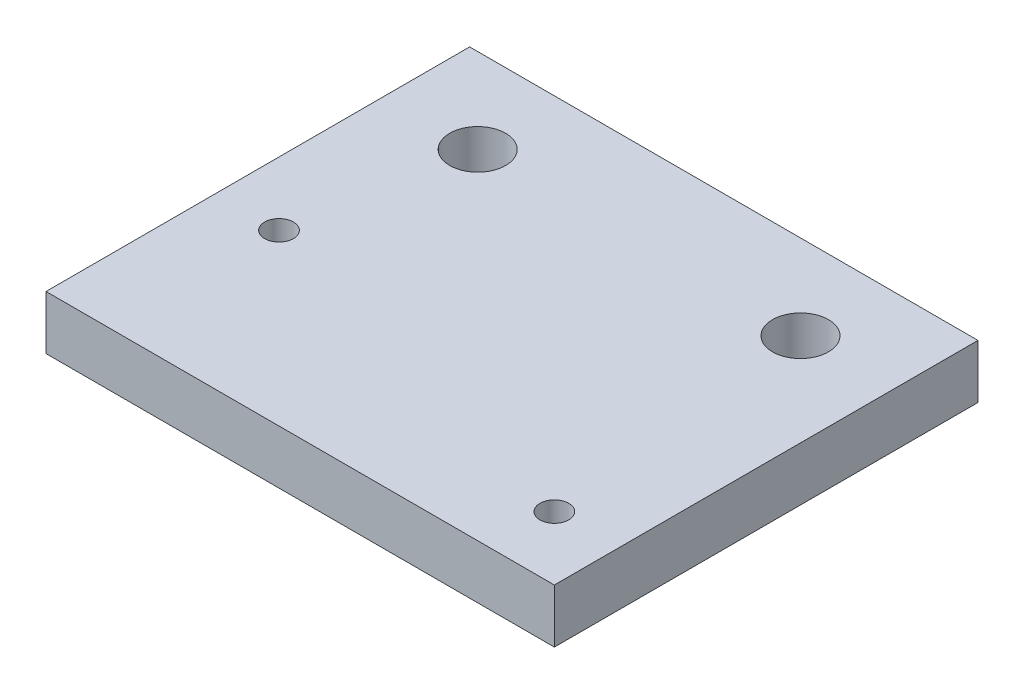
SolidWorks part; units mm, degrees
ref_plane "Front Plane" through (0, 0, 0) normal (0, 0, 1) x (1, 0, 0)
ref_plane "Top Plane" through (0, 0, 0) normal (0, 1, 0) x (1, 0, 0)
ref_plane "Right Plane" through (0, 0, 0) normal (1, 0, 0) x (0, 0, -1)
sketch "Sketch1" plane through (0, 0, 0) normal (0, 1, 0) x (1, 0, 0)
  line L0 (10.95, 40) -> (49.05, 40) construction
  line L1 (0, 50) -> (60, 50)
  line L2 (0, 50) -> (0, 0)
  line L3 (0, 0) -> (60, 0)
  line L4 (60, 50) -> (60, 0)
  line L5 (52.5, 20) -> (7.5, 20) construction
  circle A0 centre (10.95, 40) radius 3.3
  circle A1 centre (49.05, 40) radius 3.3
  circle A2 centre (7.5, 20) radius 1.7
  circle A3 centre (52.5, 7.5) radius 1.7
  point P9 (0, 0)
  point P15 (0, 0)
  point P16 (46.4465, 55)
  point P17 (30, 40)
  point P18 (30, 0)
  point P19 (30, 20)
  point P22 (30, 50)
  dimension "D3" = 3.4
  dimension "D4" = 6.6
  dimension "D1" = 50
  dimension "D2" = 60
  dimension "D5" = 38.1
  dimension "D6" = 10
  dimension "D7" = 45
  dimension "D8" = 12.5
  dimension "D9" = 20
extrude "Boss-Extrude1" add sketch "Sketch1" along normal blind 6.35
